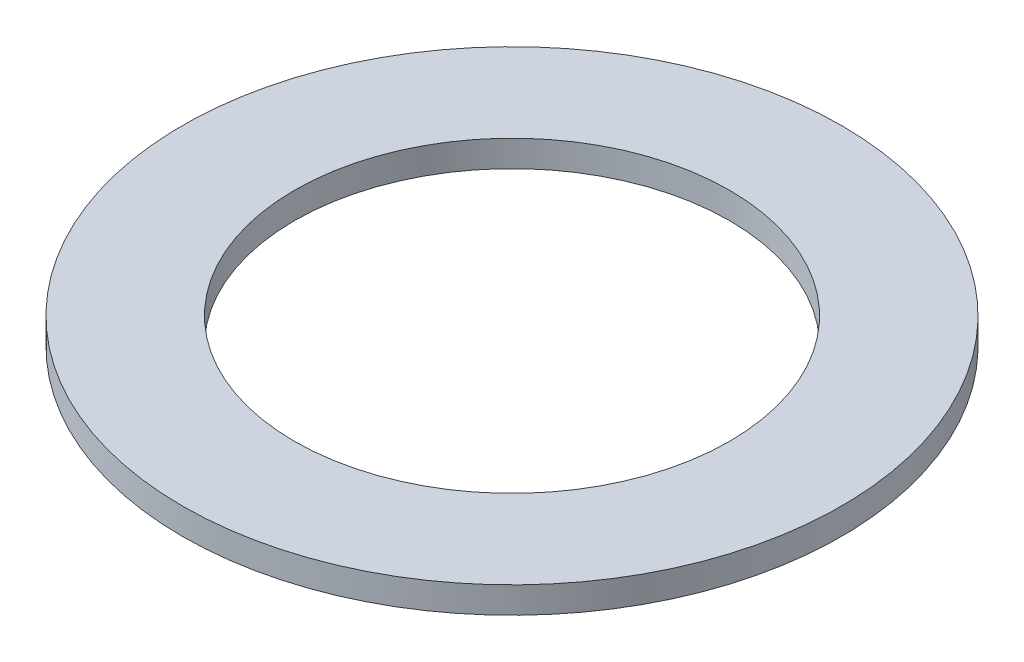
SolidWorks part; units mm, degrees
ref_plane "Front Plane" through (0, 0, 0) normal (0, 0, 1) x (1, 0, 0)
ref_plane "Top Plane" through (0, 0, 0) normal (0, 1, 0) x (1, 0, 0)
ref_plane "Right Plane" through (0, 0, 0) normal (1, 0, 0) x (0, 0, -1)
sketch "Sketch1" plane through (0, 0, 0) normal (0, 1, 0) x (1, 0, 0)
  circle A0 centre (-6.3179, 15.1141) radius 5
  circle A1 centre (-6.3179, 15.1141) radius 3.3
extrude "Boss-Extrude1" add sketch "Sketch1" along normal blind 0.4
